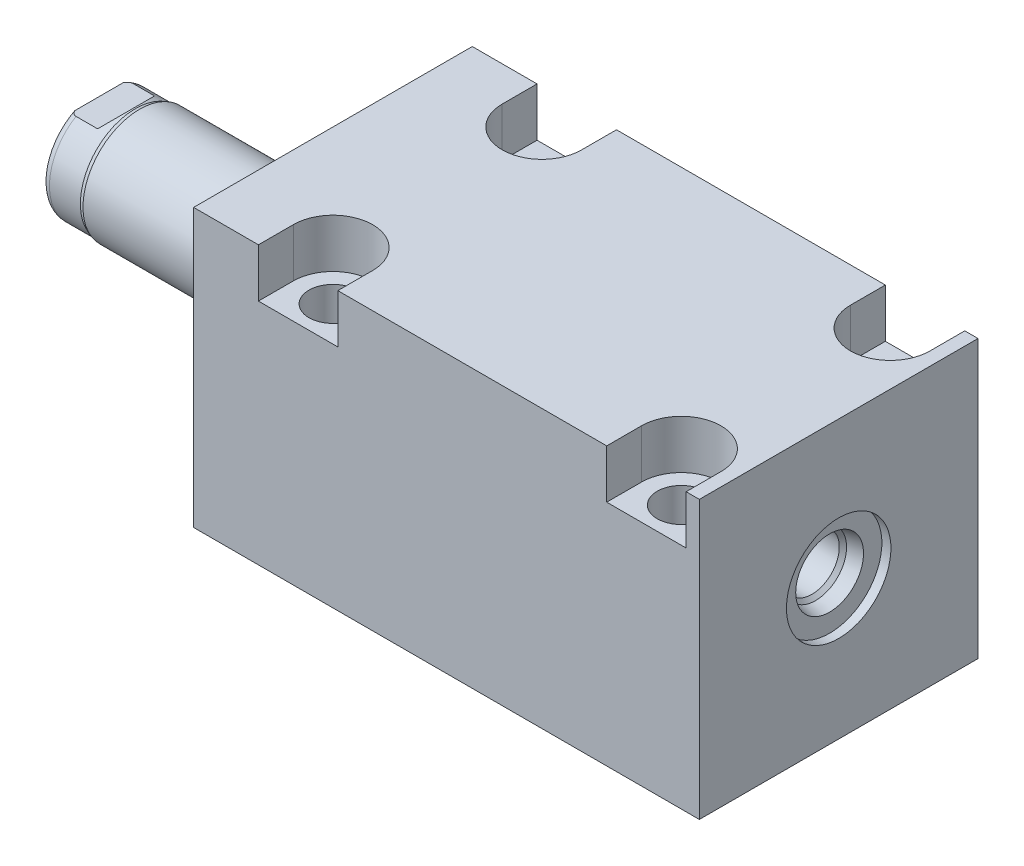
SolidWorks part; units mm, degrees
material "Alloy Steel"
ref_plane "Front Plane" through (0, 0, 0) normal (0, 0, 1) x (1, 0, 0)
ref_plane "Top Plane" through (0, 0, 0) normal (0, 1, 0) x (1, 0, 0)
ref_plane "Right Plane" through (0, 0, 0) normal (1, 0, 0) x (0, 0, -1)
ref_plane "Plane1" through (0, 0, 0) normal (1, 0, 0) x (0, 0, -1)
sketch "Sketch1" plane through (0, 0, 0) normal (1, 0, 0) x (0, 0, -1)
  line L0 (-25.4, 25.146) -> (25.4, 25.146)
  line L1 (25.4, 25.146) -> (25.4, -25.4)
  line L2 (25.4, -25.4) -> (-25.4, -25.4)
  line L3 (-25.4, -25.4) -> (-25.4, 25.146)
  line L4 (0, -24.4475) -> (0, 24.4475) construction
  dimension "D1" = 50.546
  dimension "D2" = 25.4
  dimension "D3" = 50.8
  dimension "D4" = 25.4
extrude "Extrude1" add sketch "Sketch1" along normal blind 92.202
sketch "Sketch5" plane through (0, 0, 0) normal (-1, 0, 0) x (0, 0, 1)
  circle A0 centre (0, 0) radius 17.4625
  dimension "D1" = 34.925
extrude "Extrude2" add sketch "Sketch5" along normal blind 5.969
ref_plane "Plane5" through (0, 0, 0) normal (0, -1, 0) x (0, 0, 1)
sketch "Sketch6" plane through (0, 0, 0) normal (0, -1, 0) x (0, 0, 1)
  line L0 (0, 5.969) -> (-10.3187, 5.969)
  line L1 (-10.3187, 5.969) -> (-10.3187, 42.672)
  line L2 (-10.3187, 42.672) -> (0, 42.672)
  line L3 (0, 42.672) -> (0, 5.969)
  line L4 (0, -5.7546) -> (0, 21.1709) construction
  line L5 (17.4625, 5.969) -> (-17.4625, 5.969) construction
  line L6 (25.4, -92.202) -> (-25.4, -92.202) construction
  dimension "D1" = 134.874
  dimension "D2" = 20.6375
revolve "Revolve1" add sketch "Sketch6" angle 360 about L4
ref_plane "Plane6" through (-18.5113, 3.2639, 0) normal (0, 0, 1) x (0, 1, 0)
sketch "S2D0001" plane through (-18.5113, 3.2639, 0) normal (0, 0, 1) x (0, 1, 0)
  line L0 (0, 22.225) -> (0, 9.0985)
  line L2 (1.1176, 24.1607) -> (-3.2639, 24.1607)
  line L3 (-3.2639, 24.1607) -> (-3.2639, 9.0985)
  line L4 (0, 22.225) -> (1.1176, 24.1607)
  line L5 (-3.2639, -18.5113) -> (-3.2639, 2.765) construction
  line L6 (7.0549, 24.1607) -> (-13.5826, 24.1607) construction
  line L7 (0, 9.0985) -> (-3.2639, 9.0985)
  dimension "D1" = 30
  dimension "D2" = 8.763
  dimension "D3" = 6.5278
  dimension "D4" = 15.0622
revolve "Cut-Revolve4" cut sketch "S2D0001" angle 360 about L5
ref_plane "Plane7" through (0, 0, 0) normal (0, 1, 0) x (0, 0, -1)
sketch "Sketch8" plane through (0, 0, 0) normal (0, 1, 0) x (0, 0, -1)
  line L0 (-10.3187, 35.2552) -> (-10.033, 36.0172)
  line L1 (-10.033, 36.0172) -> (-10.033, 41.656)
  line L2 (0, 12.6594) -> (0, 20.8178) construction
  line L3 (-10.3187, 35.2552) -> (-10.3187, 42.672)
  line L4 (-9.6449, 42.672) -> (-10.3187, 42.672)
  line L5 (10.3187, 42.672) -> (-10.3187, 42.672) construction
  line L6 (-10.3187, 42.672) -> (-10.3187, 5.969) construction
  arc A0 (-9.6449, 42.672) -> (-10.033, 41.656) centre (-8.509, 41.656) ccw
  dimension "D2" = 1.524
  dimension "D1" = 20.066
  dimension "D3" = 1.016
  dimension "D4" = 0.762
  dimension "D5" = 6.6548
revolve "Cut-Revolve5" cut sketch "Sketch8" angle 360 about L2
ref_plane "Plane11" through (0, 0, 0) normal (0, 0, -1) x (0, -1, 0)
sketch "Sketch12" plane through (0, 0, 0) normal (0, 0, -1) x (0, -1, 0)
  line L0 (8.5852, 42.672) -> (8.5852, 37.719)
  line L1 (8.5852, 37.719) -> (10.033, 36.2712)
  line L2 (-8.5852, 42.672) -> (-8.5852, 37.719)
  line L3 (-8.5852, 37.719) -> (-10.033, 36.2712)
  line L4 (8.5852, 42.672) -> (10.033, 42.672)
  line L5 (0, 13.7262) -> (0, 20.767) construction
  line L6 (-10.033, 36.2712) -> (-10.033, 42.672)
  line L8 (10.033, 36.0172) -> (10.033, 41.656) construction
  line L9 (10.033, 36.2712) -> (10.033, 42.672)
  line L10 (-8.5852, 42.672) -> (-10.033, 42.672)
  line L12 (9.6449, 42.672) -> (-9.6449, 42.672) construction
  dimension "D1" = 17.1704
  dimension "D2" = 4.953
  dimension "D3" = 45
extrude "Cut-Extrude4" cut sketch "Sketch12" against normal mid plane 60.96
hole_wizard "Hole2" positions "Sketch17" profile "Sketch16" legacy
sketch "Sketch17" plane through (0, 25.146, 0) normal (0, 1, 0) x (-1, 0, 0)
  line L0 (0, 0) -> (-59.3363, 0) construction
  line L1 (0, -25.4) -> (0, 25.4) construction
  point P0 (-19.05, -19.05)
  point P9 (-19.05, 19.05)
  dimension "D1" = 38.1
  dimension "D2" = 19.05
sketch "Sketch16" plane through (19.05, 25.146, -19.05) normal (1, 0, 0) x (0, 0, 1)
  line L0 (0, 0) -> (0, 50.546)
  line L1 (0, 50.546) -> (4.3688, 50.546)
  line L2 (4.3688, 50.546) -> (4.3688, 0)
  line L3 (4.3688, 0) -> (0, 0)
  line L4 (0, 110) -> (0, -10) construction
  dimension "Diameter" = 8.7376
  dimension "Depth" = 50.546
pattern_linear "LPattern1" count 2 spacing 63.5 along (1, 0, 0) of "Hole2"
sketch "Sketch18" plane through (0, 25.146, 0) normal (0, 1, 0) x (1, 0, 0)
  line L0 (0, 0) -> (50.053, 0) construction
  line L2 (92.202, -25.4) -> (0, -25.4) construction
  line L4 (89.789, -25.4) -> (75.311, -25.4)
  line L5 (11.811, -19.05) -> (11.811, -25.4)
  line L6 (26.289, -19.05) -> (26.289, -25.4)
  line L7 (75.311, -19.05) -> (75.311, -25.4)
  line L8 (89.789, 19.05) -> (89.789, 25.4)
  line L9 (26.289, -25.4) -> (11.811, -25.4)
  line L12 (26.289, 25.4) -> (11.811, 25.4)
  line L14 (75.311, 19.05) -> (75.311, 25.4)
  line L15 (26.289, 19.05) -> (26.289, 25.4)
  line L16 (11.811, 19.05) -> (11.811, 25.4)
  line L17 (89.789, 25.4) -> (75.311, 25.4)
  line L18 (89.789, -19.05) -> (89.789, -25.4)
  arc A0 (26.289, -19.05) -> (11.811, -19.05) centre (19.05, -19.05) ccw
  arc A1 (89.789, -19.05) -> (75.311, -19.05) centre (82.55, -19.05) ccw
  arc A2 (89.789, 19.05) -> (75.311, 19.05) centre (82.55, 19.05) cw
  arc A3 (26.289, 19.05) -> (11.811, 19.05) centre (19.05, 19.05) cw
  dimension "D1" = 14.478
extrude "Cut-Extrude5" cut sketch "Sketch18" against normal blind 8.89
hole_wizard "Hole3" positions "Sketch20" profile "Sketch19" legacy
sketch "Sketch20" plane through (0, -25.4, 0) normal (0, -1, 0) x (1, 0, 0)
  line L0 (0, 25.4) -> (0, -25.4) construction
  point P0 (12.7, 0)
  dimension "D1" = 12.7
sketch "Sketch19" plane through (12.7, -25.4, 0) normal (1, 0, 0) x (0, 0, -1)
  line L0 (0, 0) -> (0, 12.2569)
  line L1 (0, 12.2569) -> (1.5875, 11.303)
  line L2 (1.5875, 11.303) -> (1.5875, 1.4478)
  line L3 (1.5875, 1.4478) -> (5.6705, 1.4478)
  line L4 (5.6705, 0) -> (0, 0)
  line L5 (0, -11.3109) -> (0, 121.1557) construction
  line L6 (0, 12.2569) -> (-1.5875, 11.303) construction
  line L7 (5.6705, 1.4478) -> (5.6705, 0)
  dimension "Depth" = 11.303
  dimension "Drill Angle" = 118
  dimension "Diameter" = 3.175
  dimension "C-Bore Diameter" = 11.3411
  dimension "C-Bore Depth" = 1.4478
hole_wizard "Hole4" positions "Sketch21" profile "Sketch22" legacy
sketch "Sketch21" plane through (0, -25.4, 0) normal (0, -1, 0) x (1, 0, 0)
  point P0 (76.2, 0)
  dimension "D1" = 63.5
sketch "Sketch22" plane through (76.2, -25.4, 0) normal (1, 0, 0) x (0, 0, -1)
  line L0 (0, 0) -> (0, 14.8223)
  line L1 (0, 14.8223) -> (1.5875, 13.8684)
  line L2 (1.5875, 13.8684) -> (1.5875, 1.4478)
  line L3 (1.5875, 1.4478) -> (5.6705, 1.4478)
  line L4 (5.6705, 0) -> (0, 0)
  line L5 (0, -11.3109) -> (0, 121.1557) construction
  line L6 (0, 14.8223) -> (-1.5875, 13.8684) construction
  line L7 (5.6705, 1.4478) -> (5.6705, 0)
  dimension "Depth" = 13.8684
  dimension "Drill Angle" = 118
  dimension "Diameter" = 3.175
  dimension "C-Bore Diameter" = 11.3411
  dimension "C-Bore Depth" = 1.4478
chamfer "Chamfer1" distance 0.635 angle 45 2 edges at (76.2, -23.9522, -1.5875) (12.7, -23.9522, -1.5875)
sketch "Sketch23" plane through (0, 0, 0) normal (0, 0, 1) x (1, 0, 0)
  line L0 (12.7, -23.9522) -> (12.7, -21.4272) construction
  line L1 (10.4775, -23.9522) -> (14.9225, -23.9522) construction
  line L2 (7.0294, -23.9522) -> (18.3705, -23.9522) construction
  line L3 (7.0294, -23.9522) -> (7.0294, -25.4) construction
  circle A0 centre (8.4772, -25.4) radius 1.4478
  dimension "D1" = 2.8956
revolve "Revolve2" add sketch "Sketch23" angle 360 about L0
pattern_linear "LPattern3" count 2 spacing 63.5 along (1, 0, 0) of bodies 128
sketch "Sketch24" plane through (0, 0, 0) normal (0, 0, 1) x (1, 0, 0)
  line L0 (0, 0) -> (74.772, 0) construction
  line L1 (92.202, 9.525) -> (90.551, 9.525)
  line L2 (92.202, 25.146) -> (92.202, -25.4) construction
  line L3 (90.551, 9.525) -> (90.551, 6.1849)
  line L4 (90.551, 6.1849) -> (87.9983, 5.6423)
  line L5 (87.9983, 5.6423) -> (87.3344, 4.9784)
  line L6 (87.3344, 4.9784) -> (75.946, 4.9784)
  line L7 (75.946, 4.9784) -> (75.946, 0)
  line L8 (75.946, 0) -> (92.202, 0)
  line L9 (92.202, 0) -> (92.202, 9.525)
  dimension "D1" = 1.651
  dimension "D2" = 19.05
  dimension "D3" = 9.9568
  dimension "D4" = 16.256
  dimension "D5" = 12
  dimension "D6" = 45
  dimension "D7" = 12.3698
  dimension "D8" = 2.5527
revolve "Cut-Revolve6" cut sketch "Sketch24" angle 360 about L0
